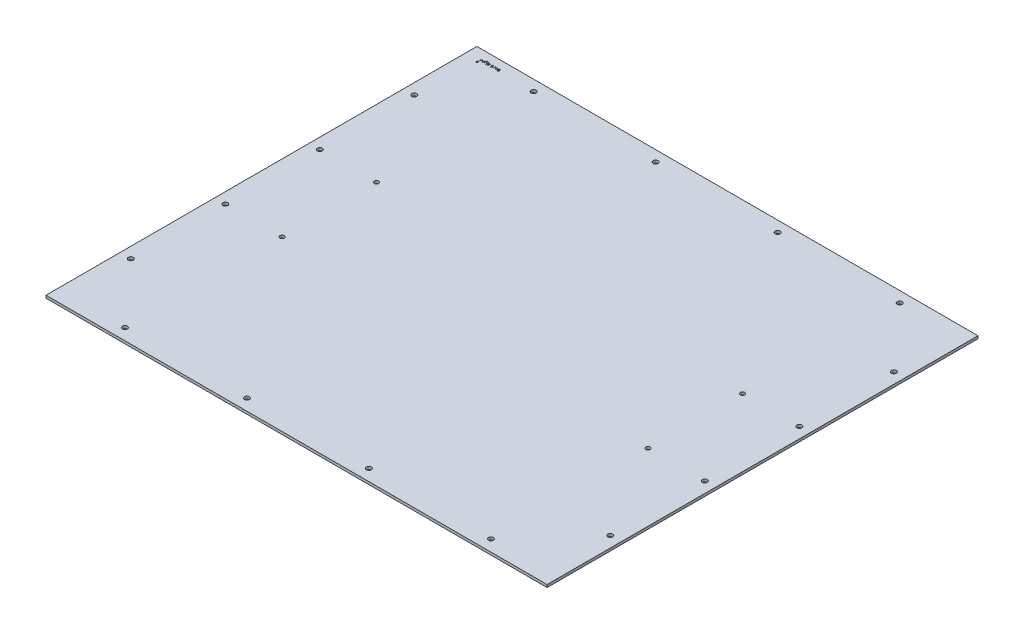
SolidWorks part; units mm, degrees
material "Acrylic (Medium-high impact)"
ref_plane "Front Plane" through (0, 0, 0) normal (0, 0, 1) x (1, 0, 0)
ref_plane "Top Plane" through (0, 0, 0) normal (0, 1, 0) x (1, 0, 0)
ref_plane "Right Plane" through (0, 0, 0) normal (1, 0, 0) x (0, 0, -1)
sketch "Sketch1" plane through (0, 0, 0) normal (0, 1, 0) x (1, 0, 0)
  line L1 (-292.1, 251.1933) -> (292.1, 251.1933)
  line L2 (-292.1, 251.1933) -> (-292.1, -251.1933)
  line L3 (-292.1, -251.1933) -> (292.1, -251.1933)
  line L4 (292.1, 251.1933) -> (292.1, -251.1933)
  line L5 (-292.1, 251.1933) -> (292.1, -251.1933) construction
  line L6 (-292.1, -251.1933) -> (292.1, 251.1933) construction
  point P0 (0, 0)
  dimension "D1" = 584.2
  dimension "D2" = 502.3866
extrude "TopPlate" add sketch "Sketch1" along normal blind 3.0734
sketch "Sketch2" plane through (0, 3.0734, 0) normal (0, 1, 0) x (1, 0, 0)
  line L0 (-213.36, 238.5949) -> (-292.1, 238.5949) construction
  line L1 (-292.1, 251.1933) -> (-292.1, -251.1933) construction
  line L2 (-213.36, 251.1933) -> (-213.36, 248.1199) construction
  line L3 (292.1, 251.1933) -> (-292.1, 251.1933) construction
  line L4 (-213.36, 248.1199) -> (-213.36, 229.0699) construction
  line L5 (-213.36, -237.8583) -> (-213.36, 238.5949) construction
  line L7 (-213.36, -247.3833) -> (-213.36, -250.5583) construction
  line L8 (-213.36, -250.5583) -> (-213.36, -253.7333) construction
  line L9 (-213.36, -247.3833) -> (-213.36, -228.3333) construction
  line L10 (-213.36, -253.7333) -> (-213.36, -256.8067) construction
  circle A0 centre (-213.36, 238.5949) radius 2.8956
  circle A1 centre (-213.36, -237.8583) radius 2.8956
  dimension "D2" = 5.7912
  dimension "D1" = 78.74
  dimension "D3" = 19.05
  dimension "D4" = 3.0734
  dimension "D5" = 19.05
  dimension "D6" = 3.175
  dimension "D7" = 3.0734
  dimension "D8" = 508
extrude "Front/RearTopHoles" cut sketch "Sketch2" against normal through all
pattern_linear "LPattern1" count 4 spacing 142.24 along (1, 0, 0) of "Front/RearTopHoles"
sketch "Sketch3" plane through (0, 3.0734, 0) normal (0, 1, 0) x (1, 0, 0)
  line L0 (-292.1, 165.6715) -> (-289.0266, 165.6715) construction
  line L1 (-292.1, 251.1933) -> (-292.1, -251.1933) construction
  line L2 (-289.0266, 165.6715) -> (-269.9766, 165.6715) construction
  line L3 (292.1, 251.1933) -> (-292.1, 251.1933) construction
  line L4 (292.1, 165.6715) -> (289.0266, 165.6715) construction
  line L5 (292.1, -251.1933) -> (292.1, 251.1933) construction
  line L6 (289.0266, 165.6715) -> (269.9766, 165.6715) construction
  line L7 (-279.5016, 251.1933) -> (-279.5016, 248.1199) construction
  line L8 (-279.5016, 248.1199) -> (-279.5016, 229.0699) construction
  circle A0 centre (-279.5016, 165.6715) radius 2.8956
  circle A1 centre (279.5016, 165.6715) radius 2.8956
  dimension "D3" = 19.05
  dimension "D1" = 5.7912
  dimension "D2" = 3.0734
  dimension "D5" = 3.0734
  dimension "D6" = 19.05
  dimension "D4" = 63.3984
extrude "Cut-Extrude2" cut sketch "Sketch3" against normal through all
pattern_linear "LPattern2" count 4 spacing 110.2021 along (0, 0, 1) of "Cut-Extrude2"
hole_wizard "#10 Clearance Hole1" positions "Sketch4" profile "Sketch5" hole size "#10" standard "ANSI Inch" end condition through all
sketch "Sketch4" plane through (0, 3.0734, 0) normal (0, 1, 0) x (1, 0, 0)
  line L0 (-292.1, 0) -> (292.1, 0) construction
  line L1 (-292.1, 251.1933) -> (-292.1, -251.1933) construction
  line L2 (292.1, -251.1933) -> (292.1, 251.1933) construction
  line L5 (0, 251.1933) -> (0, -251.1933) construction
  line L6 (292.1, 251.1933) -> (-292.1, 251.1933) construction
  line L7 (-292.1, -251.1933) -> (292.1, -251.1933) construction
  line L21 (-279.5016, 55.4694) -> (-213.36, 55.4694) construction
  line L24 (-213.36, 238.5949) -> (-213.36, 55.4694) construction
  point P27 (-213.36, 55.4694)
  point P90 (-213.36, -54.7328)
  point P99 (213.36, -54.7328)
  point P100 (213.36, 55.4694)
sketch "Sketch5" plane through (-213.36, 3.0734, -55.4694) normal (1, 0, 0) x (0, 0, 1)
  line L0 (0, 0) -> (0, 3.0734)
  line L1 (0, 3.0734) -> (2.5527, 3.0734)
  line L2 (2.5527, 3.0734) -> (2.5527, 0)
  line L5 (2.5527, 0) -> (0, 0)
  line L11 (0, -6.35) -> (0, 107.95) construction
  dimension "Thru Hole Dia." = 5.1054
  dimension "Thru Hole Depth" = 3.0734
sketch "Sketch6" plane through (0, 3.0734, 0) normal (0, 1, 0) x (1, 0, 0)
  line L0 (-213.36, 241.4905) -> (-276.606, 241.4905) construction
  line L2 (-276.606, 165.6715) -> (-276.606, 241.4905) construction
  line L3 (-276.606, 234.5018) -> (-275.59, 235.7718)
  line L4 (-275.59, 235.7718) -> (-276.098, 235.7718)
  line L5 (-276.098, 235.7718) -> (-276.098, 237.0418)
  line L6 (-276.098, 237.0418) -> (-277.114, 237.0418)
  line L7 (-277.114, 235.7718) -> (-277.114, 237.0418)
  line L8 (-277.622, 235.7718) -> (-277.114, 235.7718)
  line L9 (-276.606, 234.5018) -> (-277.622, 235.7718)
  line L10 (-276.606, 238.3118) -> (-254.0529, 238.3118) construction
  circle A0 centre (-213.36, 238.5949) radius 2.8956 construction
  circle A1 centre (-279.5016, 165.6715) radius 2.8956 construction
  text T0 "Back Right"
  point P14 (-276.606, 237.0418)
  dimension "D1" = 1.016
  dimension "D2" = 2.032
  dimension "D3" = 1.27
  dimension "D4" = 1.27
  dimension "D5" = 1.27
extrude "Cut-Extrude3" cut sketch "Sketch6" against normal blind 1.27
equation "\"Height\"= 32in"
equation "\"Width\"= 23in"
equation "\"Depth\"= 20in"
equation "\"Plexi\"= .121in"
equation "\"Boxsize\"= .75in"
equation "\"Boxinner\"= .625in"
equation "\"CornerCube\"= 0.75in"
equation "\"Cutwidth\"= .016in"
equation "\"Earsize\"= 1in + \"Cutwidth\" /2"
equation "\"Slotsize\"= 1in - \"Cutwidth\" / 2"
equation "\"InnerWidth\"= \"Width\" - 2* \"Plexi\""
equation "\"InnerHeight\"= \"Height\" -2 * \"Plexi\""
equation "\"InnerDepth\"= \"Depth\" - 2*\"Plexi\""
equation "\"RearNumHoles\"= 4"
equation "\"RearHolesBorder\"= 2.25"
equation "\"RearHoleSpacing\"= (\"Width\" - 2*\"RearHolesBorder\") / (\"RearNumHoles\"-1)"
equation "\"RearBarLength\"= (\"InnerWidth\"-2*\"CornerCube\")"
equation "\"RearTopNumHoles\"= 4"
equation "\"RearTopHolesBorder\"= 3.1"
equation "\"RearTopHolesSpacing\"= (\"Width\" - 2*\"RearTopHolesBorder\") / (\"RearTopNumHoles\"-1)"
equation "\"SideVertNumHoles\"= 4"
equation "\"SideVertHolesBorder\"= \"CornerCube\"+\"FingerLength\"+1.50"
equation "\"SideVertHoleSpacing\"= (\"InnerHeight\" - 2*\"SideVertHolesBorder\") / (\"SideVertNumHoles\"-1)"
equation "\"RivetDia\"= .228in"
equation "\"SlotDepth\"= \"Plexi\" + 0.75in + .005in"
equation "\"SideSlotWidth\"= \"Plexi\"+.005in"
equation "\"SidePanelVertSpacing\"= (\"Height\"-2*(1.75-\"Plexi\")) / 5"
equation "\"BottomPanelSideHoleSpacing\"= (\"InnerDepth\"-2*(1.75-\"Plexi\")) / 4"
equation "\"D1@Sketch1\"=\"Width\""
equation "\"D2@Sketch1\"=\"TopDepth\""
equation "\"FrontDoorGap\"= .1in"
equation "\"TopDepth\"= \"Depth\"-\"DoorPlexi\"-\"FrontDoorGap\""
equation "\"D1@Sketch2\"=\"RearTopHolesBorder\""
equation "\"D2@Sketch2\"=\"RivetDia\""
equation "\"D3@Sketch2\"=\"Boxsize\""
equation "\"D4@Sketch2\"=\"Plexi\""
equation "\"D5@Sketch2\"=\"Boxsize\""
equation "\"MagnetThickness\"= 0.125in"
equation "\"MagnetDiameter\"= 12mm"
equation "\"D6@Sketch2\"=\"MagnetThickness\""
equation "\"DoorPlexi\"= \"Plexi\""
equation "\"D7@Sketch2\"=\"DoorPlexi\""
equation "\"D8@Sketch2\"=\"Depth\""
equation "\"D3@LPattern1\"=\"RearTopHolesSpacing\""
equation "\"D1@LPattern1\"=\"RearTopNumHoles\""
equation "\"D1@Sketch3\"=\"RivetDia\""
equation "\"D2@Sketch3\"=\"Plexi\""
equation "\"D3@Sketch3\"=\"Boxsize\""
equation "\"FingerLength\"= 1.125in"
equation "\"SideTopNumHoles\"= 4"
equation "\"SideTopHoleOffset\"=\"CornerCube\"+\"FingerLength\"+\"Plexi\"+.5"
equation "\"SideTopHoleSpacing\"= (\"TopBarDepth\"-2*\"SideTopHoleOffset\") / (\"SideTopNumHoles\"-1)"
equation "\"SideHorizNumHoles\"= 4"
equation "\"SideHorizHoleBorder\"= 1.50"
equation "\"SideHorizHoleSpacing\"= (\"TopBarDepth\"-2*\"SideHorizHoleBorder\") / (\"SideHorizNumHoles\"-1)"
equation "\"TopBarDepth\"= \"Depth\"-\"DoorPlexi\"-\"Plexi\"-2*\"MagnetThickness\"-2*\"CornerCube\""
equation "\"D4@Sketch3\"=\"SideTopHoleOffset\""
equation "\"D3@LPattern2\"=\"SideTopHoleSpacing\""
equation "\"D1@LPattern2\"=\"SideTopNumHoles\""
equation "\"D5@Sketch3\"=\"Plexi\""
equation "\"D6@Sketch3\"=\"CornerCube\""
equation "\"EBWidth\"= 9in"
equation "\"BasePlateThickness\"= 0.5in"
equation "\"BasePlateWidth\"= \"Width\"+\"EBWidth\"-2*\"Plexi\""
equation "\"BasePlateDepth\"= \"TopBarDepth\"+2*\"CornerCube\""
equation "\"BoxsizeHalf\"= \"Boxsize\"/2"
equation "\"FingerWidth\"= .625in"
equation "\"SideVertBarLength\"=\"Height\"-\"BasePlateThickness\"-2*\"CornerCube\"-\"Plexi\""
equation "\"RearSideVertNumHoles\"= 4"
equation "\"RearSideVertHolesBorder\"= 2.4"
equation "\"RearSideVertHoleSpacing\"= (\"InnerHeight\" - 2*\"RearSideVertHolesBorder\") / (\"RearSideVertNumHoles\"-1)"
equation "\"CoolerDepth\"= 12in"
equation "\"ShelfGap\"= 0.5in"
equation "\"ShelfDepth\"= \"TopBarDepth\"+\"CornerCube\"-\"CoolerDepth\""
equation "\"ShelfBarDepth\"=\"ShelfDepth\"-2*\"CornerCube\""
equation "\"ShelfWidth\"= \"EBWidth\"-\"ShelfGap\""
equation "\"ShelfBarWidth\"= \"EBWidth\"-\"Boxsize\""
equation "\"ShelfBarWidthShort\"= \"ShelfBarWidth\"-\"Boxsize\"-\"ShelfGap\""
equation "\"IntakeWidth\"=4in"
equation "\"IntakeHeight\"=2in"
equation "\"ExhaustWidth\"=4in"
equation "\"ExhaustHeight\"=2in"
equation "\"VentSpacing\"=7in"
equation "\"AngleBracketLength\"=20mm"
equation "\"AngleBracketWidth\"=.5in"
equation "\"AngleBracketThickness\"=.125in"
equation "\"AngleBracketHolePos\"=15mm"
equation "\"AngleBracketHoleDia\"=\"Rivet3_16Dia\""
equation "\"ShelfBarAngleHole\"=\"ShelfGap\"+\"Boxsize\"+\"AngleBracketHolePosShort\""
equation "\"D1@TopPlate\"=\"Plexi\""
